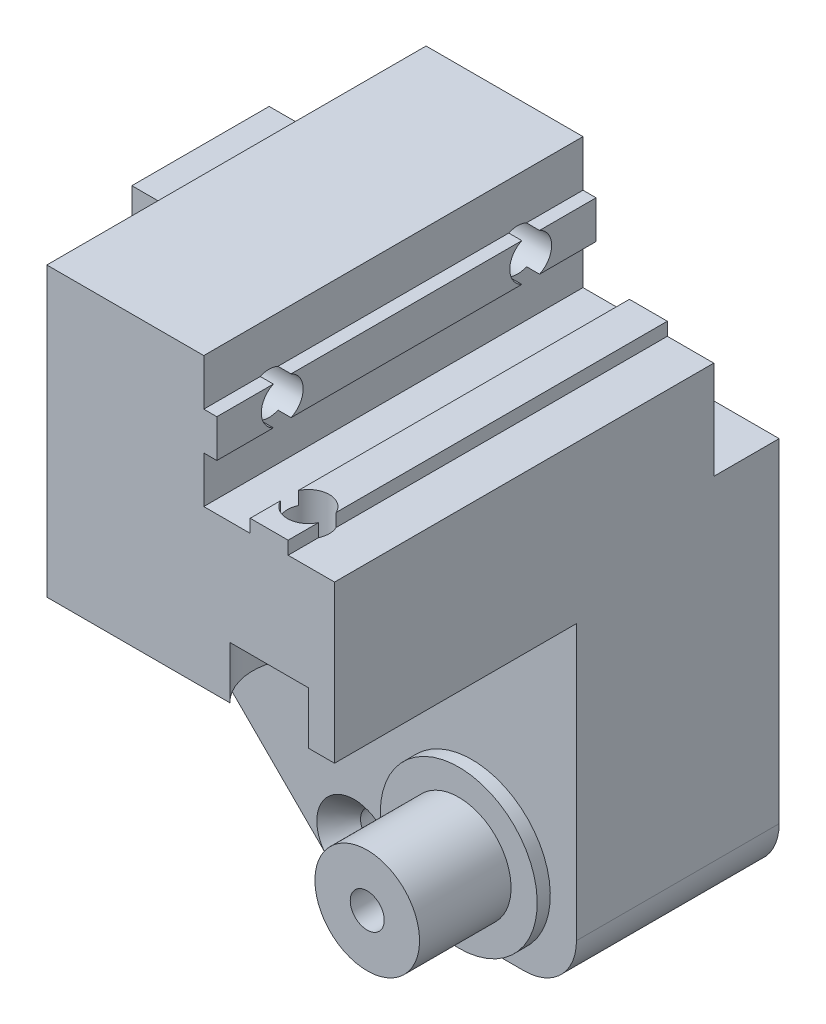
SolidWorks part; units mm, degrees
ref_plane "Plan de face" through (0, 0, 0) normal (0, 0, 1) x (1, 0, 0)
ref_plane "Plan de dessus" through (0, 0, 0) normal (0, 1, 0) x (1, 0, 0)
ref_plane "Plan de droite" through (0, 0, 0) normal (1, 0, 0) x (0, 0, -1)
sketch "Base Sketchup" plane through (0, 0, 0) normal (0, 0, 1) x (1, 0, 0)
  line L1 (-17, -18.5) -> (17, -18.5)
  line L2 (-17, -18.5) -> (-17, 18.5)
  line L3 (-17, 18.5) -> (17, 18.5)
  line L4 (17, -18.5) -> (17, 18.5)
  point P7 (0, 18.5)
  point P8 (-17, 0)
  dimension "D1" = 37
  dimension "D2" = 34
extrude "Base Extrusion" add sketch "Base Sketchup" along normal blind 15.5
sketch "Fix Sketchup" plane through (0, 0, 0) normal (0, 0, -1) x (-1, 0, 0)
  line L0 (17, 18.5) -> (17, -18.5) construction
  line L2 (17, 18.5) -> (13.45, 18.5)
  line L4 (13.45, 18.5) -> (13.45, 19.5)
  line L5 (13.45, 19.5) -> (10.55, 19.5)
  line L6 (10.55, 19.5) -> (10.55, 18.5)
  line L7 (10.55, 18.5) -> (7, 18.5)
  line L8 (7, 18.5) -> (7, 22.05)
  line L10 (7, 22.05) -> (8, 22.05)
  line L11 (-5, 6.5) -> (17, 6.5)
  line L12 (8, 22.05) -> (8, 24.95)
  line L13 (17, 6.5) -> (17, 18.5)
  line L14 (8, 24.95) -> (7, 24.95)
  line L15 (7, 24.95) -> (7, 28.5)
  line L16 (7, 28.5) -> (-5, 28.5)
  line L17 (-5, 28.5) -> (-5, 6.5)
  line L19 (17, -18.5) -> (-17, -18.5) construction
  dimension "D1" = 37
  dimension "D2" = 10
  dimension "D3" = 1
  dimension "D5" = 3.55
  dimension "D6" = 12
  dimension "D7" = 12
extrude "Fix Extrusion" add sketch "Fix Sketchup" against normal blind 34 separate body
sketch "Ball Place Sketchup" plane through (0, -18.5, 0) normal (0, -1, 0) x (1, 0, 0)
  line L0 (-12.25, 0) -> (-12.25, 8.25)
  line L1 (-17, 0) -> (17, 0) construction
  line L2 (-12.25, 8.25) -> (-11.75, 8.25)
  line L3 (-11.75, 8.25) -> (-11.75, 9.25)
  line L4 (-11.75, 9.25) -> (-12.25, 9.25)
  line L5 (-12.25, 9.25) -> (-12.25, 11.5)
  line L6 (-12.25, 11.5) -> (12.25, 11.5)
  line L7 (12.25, 11.5) -> (12.25, 9.25)
  line L8 (12.25, 9.25) -> (11.75, 9.25)
  line L9 (11.75, 9.25) -> (11.75, 8.25)
  line L10 (11.75, 8.25) -> (12.25, 8.25)
  line L11 (12.25, 8.25) -> (12.25, 0)
  line L12 (12.25, 0) -> (-12.25, 0)
  line L13 (-17, 15.5) -> (17, 15.5) construction
  point P15 (0, 11.5)
  point P18 (0, 15.5)
  dimension "D1" = 24.5
  dimension "D2" = 0.5
  dimension "D3" = 1
  dimension "D4" = 2.25
  dimension "D5" = 11.5
extrude "Ball Extrusion" cut sketch "Ball Place Sketchup" against normal blind 29
hole_wizard "Fraisage pour vis à tête fraisée bombée #41" positions "Esquisse3D1" profile "Esquisse12" countersink size "#4" standard "Ansi Inch"
sketch3d "Esquisse3D1"
  line L0 (-17, -18.5, 15.5) -> (17, -18.5, 15.5) construction
  point P0 (0, -16.5, 15.5)
  point P9 (0, -18.5, 15.5)
  dimension "D1" = 2
sketch "Esquisse12" plane through (0, -16.5, 15.5) normal (1, 0, 0) x (0, -1, 0)
  line L0 (0, 0) -> (0, 15.5)
  line L1 (0, 15.5) -> (1.3, 15.5)
  line L2 (1.3, 15.5) -> (1.3, 1.7917)
  line L3 (1.3, 1.7917) -> (2.8575, 0)
  line L5 (2.8575, 0) -> (0, 0)
  line L6 (-1.3, 1.7917) -> (-2.8575, 0) construction
  line L11 (0, -6.35) -> (0, 107.95) construction
  dimension "Diamètre du perçage jusqu'au prochain" = 2.6
  dimension "Profondeur du perçage jusqu'au prochain" = 15.5
  dimension "Diamètre du fraisage entrant" = 5.715
  dimension "Angle du fraisage entrant" = 82
sketch "Ball Bearing Base Sketchup" plane through (0, 0, 15.5) normal (0, 0, 1) x (1, 0, 0)
  line L0 (-17, 18.5) -> (-17, -18.5) construction
  line L2 (-17, -18.5) -> (-2.0409, -18.5) construction
  circle A0 centre (-9, -12.5) radius 6
  dimension "D1" = 12
  dimension "D2" = 8
  dimension "D3" = 6
extrude "Ball Bearing Base Extrusion" add sketch "Ball Bearing Base Sketchup" along normal blind 1
sketch "Ball Bearing Sketchup" plane through (0, 0, 16.5) normal (0, 0, 1) x (1, 0, 0)
  circle A0 centre (-9, -12.5) radius 4
  circle A1 centre (-9, -12.5) radius 6 construction
  dimension "D1" = 8
extrude "Ball Bearing Extrusion" add sketch "Ball Bearing Sketchup" along normal blind 7
sketch "Ball Bearing Fix Sketchup" plane through (0, 0, 23.5) normal (0, 0, 1) x (1, 0, 0)
  circle A0 centre (-9, -12.5) radius 1.3
  circle A1 centre (-9, -12.5) radius 4 construction
  dimension "D1" = 2.6
extrude "Ball Bearing Fix Hole" cut sketch "Ball Bearing Fix Sketchup" against normal up to surface (12 mm away) up to face at (1.3, -16.5, 11.5)
sketch "Esquisse10" plane through (0, 0, 11.5) normal (0, 0, -1) x (-1, 0, 0)
  line L0 (12.25, -2) -> (12.25, 10.5)
  line L1 (12.25, 10.5) -> (-12.25, 10.5)
  line L2 (-12.25, 10.5) -> (-12.25, -2)
  line L3 (-12.25, 10.5) -> (12.25, 10.5) construction
  line L4 (12.25, 10.5) -> (12.25, -18.5) construction
  line L5 (-12.25, 10.5) -> (-12.25, -18.5) construction
  arc A0 (12.25, -2) -> (-12.25, -2) centre (0, -2) ccw
  dimension "D1" = 12.25
  dimension "D2" = 12.5
extrude "Boss.-Extru.5" add sketch "Esquisse10" along normal up to surface (11.5 mm away) up to face at (0, -2, 0)
sketch "Esquisse11" plane through (0, 0, 8.25) normal (0, 0, -1) x (-1, 0, 0)
  line L0 (-11.75, 1.4641) -> (-11.75, -18.5) construction
  line L1 (11.75, -2) -> (12.25, -2)
  line L2 (12.25, 10.25) -> (-12.25, 10.25)
  line L3 (-11.75, -2) -> (-12.25, -2)
  line L5 (12.25, -2) -> (12.25, 10.25)
  line L6 (12.25, -2) -> (12.25, -18.5) construction
  line L7 (-12.25, -2) -> (-12.25, 10.25)
  line L8 (-12.25, -2) -> (-12.25, -18.5) construction
  arc A0 (-11.75, -2) -> (11.75, -2) centre (0, -2) cw
  arc A1 (12.25, -2) -> (-12.25, -2) centre (0, -2) ccw construction
  dimension "D1" = 11.75
  dimension "D2" = 12.25
extrude "Boss.-Extru.6" add sketch "Esquisse11" against normal up to surface (1 mm away) up to face at (12.0311, -9.3795, 9.25)
ref_plane "Symetry Plan" through (-10, 0, 0) normal (1, 0, 0) x (0, 0, -1)
sketch "Esquisse13" plane through (17, 0, 0) normal (1, 0, 0) x (0, 0, -1)
  line L0 (0, -18.5) -> (0, 18.5) construction
  line L1 (-5, 11) -> (0, 11)
  line L2 (-5, 11) -> (-5, 28.5)
  line L3 (-5, 28.5) -> (0, 28.5)
  line L4 (0, 11) -> (0, 28.5)
  line L5 (-15.5, 18.5) -> (0, 18.5) construction
  line L6 (-34, 28.5) -> (0, 28.5) construction
  dimension "D1" = 5
  dimension "D2" = 7.5
extrude "Enlèv. mat.-Extru.1" cut sketch "Esquisse13" against normal through all
fillet "Congé2" radius 4 1 edges at (-17, -18.5, 7.75)
sketch "Esquisse14" plane through (0, 0, 15.5) normal (0, 0, 1) x (1, 0, 0)
  line L0 (2, -18.5) -> (17, -3.5)
  line L1 (2.0409, -18.5) -> (17, -18.5) construction
  line L2 (17, -18.5) -> (17, 18.5) construction
  line L3 (17, -3.5) -> (17, -18.5)
  line L4 (17, -18.5) -> (2, -18.5)
  dimension "D1" = 15
  dimension "D2" = 15
extrude "Enlèv. mat.-Extru.2" cut sketch "Esquisse14" against normal through all
fillet "Congé4" radius 2 1 edges at (17, -3.5, 7.75)
sketch "Esquisse16" plane through (5, 0, 0) normal (1, 0, 0) x (0, 0, -1)
  line L0 (-34, 28.5) -> (-5, 28.5) construction
  line L1 (-34, 28.5) -> (-34, 6.5) construction
  line L2 (-5, 28.5) -> (-5, 18.5) construction
  circle A0 centre (-29, 23.5) radius 1.6
  circle A1 centre (-10, 23.5) radius 1.6
  dimension "D1" = 3.2
  dimension "D2" = 5
  dimension "D3" = 5
  dimension "D4" = 5
extrude "MakerBeamInteriorHoles1" cut sketch "Esquisse16" against normal through all
sketch "Esquisse17" plane through (5, 0, 0) normal (1, 0, 0) x (0, 0, -1)
  circle A0 centre (-29, 23.5) radius 4.25
  circle A1 centre (-10, 23.5) radius 4.25
  circle A2 centre (-29, 23.5) radius 1.6 construction
  circle A3 centre (-10, 23.5) radius 1.6 construction
  dimension "D1" = 8.5
extrude "MakerBeamInteriorHoles2" cut sketch "Esquisse17" against normal blind 4
sketch "Esquisse18" plane through (0, 6.5, 0) normal (0, -1, 0) x (-1, 0, 0)
  line L0 (17, -34) -> (17, -15.5) construction
  line L1 (-5, -34) -> (17, -34) construction
  circle A0 centre (12, -31) radius 1.6
  dimension "D1" = 3.2
  dimension "D2" = 5
  dimension "D3" = 3
extrude "MakerBeamFrontHole1" cut sketch "Esquisse18" against normal through all
sketch "Esquisse19" plane through (0, 6.5, 0) normal (0, -1, 0) x (-1, 0, 0)
  circle A0 centre (12, -31) radius 4.25
  circle A2 centre (12, -31) radius 1.6 construction
  dimension "D1" = 8.5
extrude "MakerBeamFrontHole2" cut sketch "Esquisse19" against normal blind 4
ref_plane "Plan1" through (20, 0, 0) normal (1, 0, 0) x (0, 0, -1)
mirror "Symétrie2" about plane through (20, 0, 0) normal (1, 0, 0) of bodies 125
sketch "Esquisse20" plane through (0, 0, 34) normal (0, 0, 1) x (1, 0, 0)
  line L0 (20, -18.7) -> (20, 18.7) construction
  line L1 (-17, 28.5) -> (20, 28.5)
  line L2 (-17, 28.5) -> (-17, -18.5)
  line L3 (-17, -18.5) -> (20, -18.5)
  line L4 (20, 28.5) -> (20, -18.5)
  line L5 (-9, -18.5) -> (-2.0409, -18.5) construction
  line L6 (-7, 28.5) -> (5, 28.5) construction
  line L7 (-17, 6.5) -> (-17, -14.5) construction
extrude "Enlèv. mat.-Extru.7" cut sketch "Esquisse20" against normal through all
